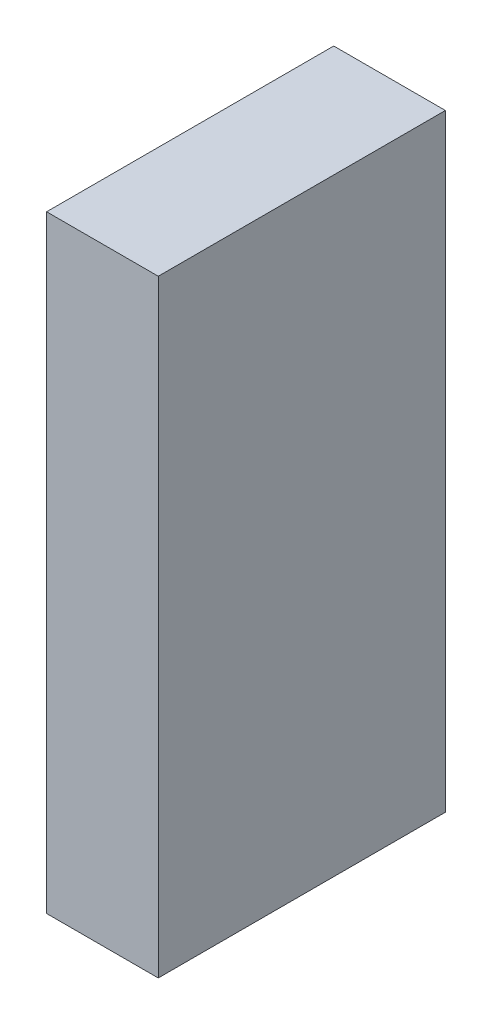
SolidWorks part; units mm, degrees
material "ABS"
ref_plane "Front Plane" through (0, 0, 0) normal (0, 0, 1) x (1, 0, 0)
ref_plane "Top Plane" through (0, 0, 0) normal (0, 1, 0) x (1, 0, 0)
ref_plane "Right Plane" through (0, 0, 0) normal (1, 0, 0) x (0, 0, -1)
sketch "Sketch1" plane through (0, 0, 0) normal (1, 0, 0) x (0, 0, -1)
  line L13 (0, 0) -> (18, 0)
  line L14 (0, 0) -> (0, 38.1)
  line L15 (0, 38.1) -> (18, 38.1)
  line L16 (18, 0) -> (18, 38.1)
  dimension "D1" = 18
  dimension "D2" = 38.1
extrude "Boss-Extrude1" add sketch "Sketch1" along normal blind 7
equation "\"1c\"=10"
